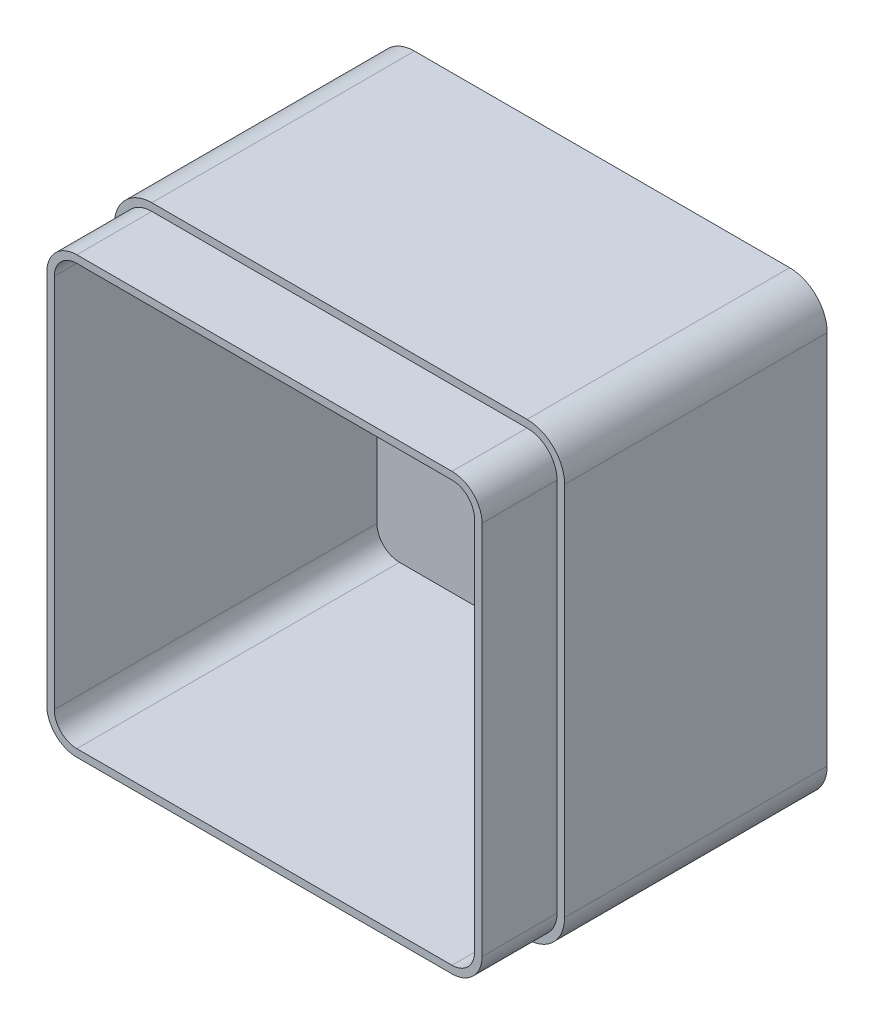
SolidWorks part; units mm, degrees
ref_plane "Front Plane" through (0, 0, 0) normal (0, 0, 1) x (1, 0, 0)
ref_plane "Top Plane" through (0, 0, 0) normal (0, 1, 0) x (1, 0, 0)
ref_plane "Right Plane" through (0, 0, 0) normal (1, 0, 0) x (0, 0, -1)
sketch "Sketch1" plane through (0, 0, 0) normal (0, 0, 1) x (1, 0, 0)
  line L1 (-60, 60) -> (60, 60)
  line L2 (-60, 60) -> (-60, -60)
  line L3 (-60, -60) -> (60, -60)
  line L4 (60, 60) -> (60, -60)
  dimension "D1" = 120
  dimension "D2" = 120
  dimension "D3" = 60
  dimension "D4" = 60
extrude "Boss-Extrude1" add sketch "Sketch1" along normal blind 90
fillet "Fillet1" radius 10 4 edges at (60, -60, 45) (-60, -60, 45) (-60, 60, 45) (60, 60, 45)
shell "Shell1" thickness 4
sketch "Sketch2" plane through (0, 0, 90) normal (0, 0, 1) x (1, 0, 0)
  line L0 (-50, -58) -> (50, -58)
  line L1 (58, -50) -> (58, 50)
  line L2 (50, 58) -> (-50, 58)
  line L3 (-58, 50) -> (-58, -50)
  line L4 (-50, -60) -> (50, -60)
  line L5 (60, -50) -> (60, 50)
  line L6 (50, 60) -> (-50, 60)
  line L7 (-60, 50) -> (-60, -50)
  line L8 (-50, -60) -> (50, -60)
  line L9 (60, -50) -> (60, 50)
  line L10 (50, 60) -> (-50, 60)
  line L11 (-60, 50) -> (-60, -50)
  arc A0 (50, -58) -> (58, -50) centre (50, -50) ccw
  arc A1 (58, 50) -> (50, 58) centre (50, 50) ccw
  arc A2 (-50, 58) -> (-58, 50) centre (-50, 50) ccw
  arc A3 (-58, -50) -> (-50, -58) centre (-50, -50) ccw
  arc A4 (50, -60) -> (60, -50) centre (50, -50) ccw
  arc A5 (60, 50) -> (50, 60) centre (50, 50) ccw
  arc A6 (-50, 60) -> (-60, 50) centre (-50, 50) ccw
  arc A7 (-60, -50) -> (-50, -60) centre (-50, -50) ccw
  arc A8 (50, -60) -> (60, -50) centre (50, -50) ccw
  arc A9 (60, 50) -> (50, 60) centre (50, 50) ccw
  arc A10 (-50, 60) -> (-60, 50) centre (-50, 50) ccw
  arc A11 (-60, -50) -> (-50, -60) centre (-50, -50) ccw
  dimension "D1" = 0
  dimension "D2" = 2
extrude "Cut-Extrude1" cut sketch "Sketch2" against normal blind 20
